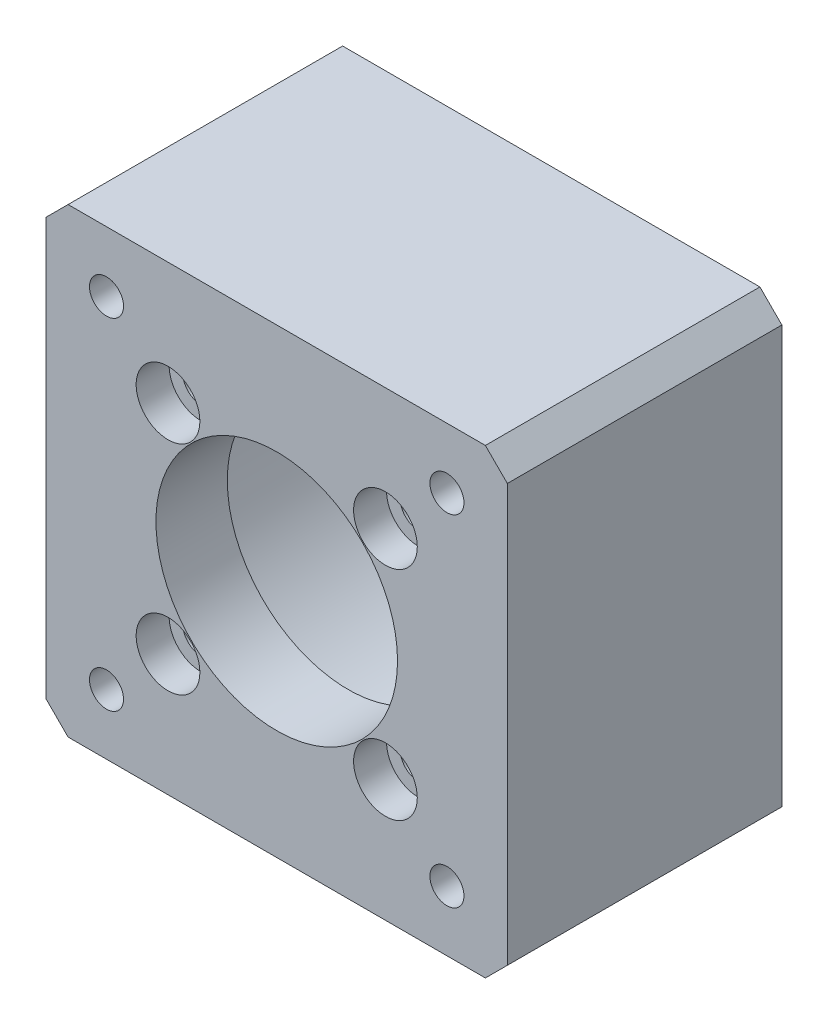
SolidWorks part; units mm, degrees
ref_plane "Front Plane" through (0, 0, 0) normal (0, 0, 1) x (1, 0, 0)
ref_plane "Top Plane" through (0, 0, 0) normal (0, 1, 0) x (1, 0, 0)
ref_plane "Right Plane" through (0, 0, 0) normal (1, 0, 0) x (0, 0, -1)
sketch "Sketch1" plane through (0, 0, 0) normal (0, 0, 1) x (1, 0, 0)
  line L1 (-21, 21) -> (21, 21)
  line L2 (-21, 21) -> (-21, -21)
  line L3 (-21, -21) -> (21, -21)
  line L4 (21, 21) -> (21, -21)
  line L5 (-21, 21) -> (21, -21) construction
  line L6 (-21, -21) -> (21, 21) construction
  circle A1 centre (-15.5, 15.5) radius 1.55
  circle A2 centre (15.5, 15.5) radius 1.55
  circle A3 centre (15.5, -15.5) radius 1.55
  circle A4 centre (-15.5, -15.5) radius 1.55
  point P18 (0, 0)
  dimension "D4" = 3.1
  dimension "D2" = 42
  dimension "D3" = 42
  dimension "D6" = 31
  dimension "D5" = 4
extrude "Boss-Extrude1" add sketch "Sketch1" along normal blind 25
sketch "Sketch2" plane through (0, 0, 25) normal (0, 0, 1) x (1, 0, 0)
  line L0 (0, 0) -> (17.5497, 0) construction
  line L1 (0, 0) -> (9.8995, 9.8995) construction
  circle A0 centre (9.8995, 9.8995) radius 1.65
  circle A1 centre (9.8995, -9.8995) radius 1.65
  circle A2 centre (-9.8995, -9.8995) radius 1.65
  circle A3 centre (-9.8995, 9.8995) radius 1.65
  circle A4 centre (0, 0) radius 11
  point P14 (0, 0)
  dimension "D2" = 3.3
  dimension "D1" = 45
  dimension "D3" = 14
  dimension "D4" = 4
extrude "Cut-Extrude1" cut sketch "Sketch2" against normal up to surface (25 mm away) up to face at (0, 0, 0)
sketch "Sketch3" plane through (0, 0, 25) normal (0, 0, 1) x (1, 0, 0)
  circle A0 centre (9.8995, 9.8995) radius 2.9
  circle A1 centre (9.8995, -9.8995) radius 2.9
  circle A2 centre (-9.8995, -9.8995) radius 2.9
  circle A3 centre (-9.8995, 9.8995) radius 2.9
  circle A4 centre (9.8995, -9.8995) radius 1.65 construction
  point P12 (0, 0)
  dimension "D1" = 5.8
  dimension "D2" = 4
extrude "Cut-Extrude2" cut sketch "Sketch3" against normal blind 3
chamfer "Chamfer1" distance 2 angle 45 4 edges at (-21, -21, 12.5) (21, -21, 12.5) (21, 21, 12.5) (-21, 21, 12.5)
sketch "Sketch4" plane through (0, 0, 0) normal (0, 0, -1) x (-1, 0, 0)
  circle A1 centre (0, 0) radius 18.15
  dimension "D1" = 36.3
extrude "Cut-Extrude3" cut sketch "Sketch4" against normal blind 18.5
ref_plane "基准面1" through (0, 0, 25) normal (0, 0, 1) x (1, 0, 0)
sketch "草图1" plane through (0, 0, 0) normal (0, 0, 1) x (1, 0, 0)
  line L0 (-15.5, 12.2091) -> (-12.65, 13.8546)
  line L1 (-12.65, 13.8546) -> (-12.65, 17.1454)
  line L2 (-12.65, 17.1454) -> (-15.5, 18.7909)
  line L3 (-15.5, 18.7909) -> (-18.35, 17.1454)
  line L4 (-18.35, 17.1454) -> (-18.35, 13.8546)
  line L5 (-18.35, 13.8546) -> (-15.5, 12.2091)
  line L6 (15.5, -12.2091) -> (12.65, -13.8546)
  line L7 (15.5, 18.7909) -> (12.65, 17.1454)
  line L8 (12.65, 17.1454) -> (12.65, 13.8546)
  line L9 (12.65, 13.8546) -> (15.5, 12.2091)
  line L10 (15.5, 12.2091) -> (18.35, 13.8546)
  line L11 (18.35, 13.8546) -> (18.35, 17.1454)
  line L12 (18.35, 17.1454) -> (15.5, 18.7909)
  line L14 (12.65, -13.8546) -> (12.65, -17.1454)
  line L15 (12.65, -17.1454) -> (15.5, -18.7909)
  line L23 (15.5, -18.7909) -> (18.35, -17.1454)
  line L30 (18.35, -17.1454) -> (18.35, -13.8546)
  line L31 (18.35, -13.8546) -> (15.5, -12.2091)
  line L34 (-15.5, -12.2091) -> (-18.35, -13.8546)
  line L35 (-18.35, -13.8546) -> (-18.35, -17.1454)
  line L36 (-18.35, -17.1454) -> (-15.5, -18.7909)
  line L37 (-15.5, -18.7909) -> (-12.65, -17.1454)
  line L38 (-12.65, -17.1454) -> (-12.65, -13.8546)
  line L39 (-12.65, -13.8546) -> (-15.5, -12.2091)
  circle A0 centre (-15.5, 15.5) radius 2.85 construction
  circle A1 centre (15.5, 15.5) radius 2.85 construction
  circle A2 centre (15.5, -15.5) radius 2.85 construction
  circle A3 centre (-15.5, -15.5) radius 2.85 construction
  circle A4 centre (-15.5, 15.5) radius 1.55 construction
  circle A7 centre (15.5, -15.5) radius 1.55 construction
  circle A8 centre (-15.5, -15.5) radius 1.55 construction
  circle A9 centre (15.5, 15.5) radius 1.55 construction
  dimension "D1" = 5.7
  dimension "D2" = 5.7
  dimension "D3" = 5.7
  dimension "D4" = 5.7
extrude "切除-拉伸1" cut sketch "草图1" along normal blind 4
